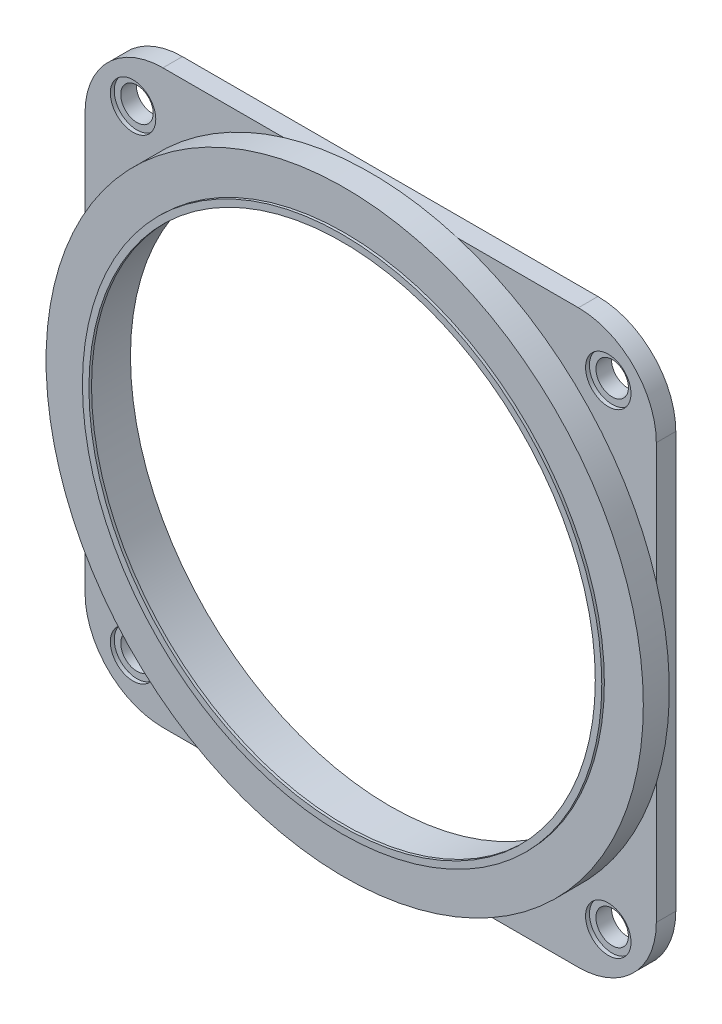
SolidWorks part; units mm, degrees
ref_plane "Alzado" through (0, 0, 0) normal (0, 0, 1) x (1, 0, 0)
ref_plane "Planta" through (0, 0, 0) normal (0, 1, 0) x (1, 0, 0)
ref_plane "Vista lateral" through (0, 0, 0) normal (1, 0, 0) x (0, 0, -1)
sketch "Croquis1" plane through (0, 0, 0) normal (0, 0, 1) x (1, 0, 0)
  line L1 (-16, 22) -> (16, 22)
  line L2 (-22, 16) -> (-22, -16)
  line L3 (-16, -22) -> (16, -22)
  line L4 (22, 16) -> (22, -16)
  line L5 (-22, 22) -> (22, -22) construction
  line L6 (-22, -22) -> (22, 22) construction
  arc A0 (-22, -16) -> (-16, -22) centre (-16, -16) ccw
  arc A1 (16, -22) -> (22, -16) centre (16, -16) ccw
  arc A2 (16, 22) -> (22, 16) centre (16, 16) cw
  arc A3 (-16, 22) -> (-22, 16) centre (-16, 16) ccw
  point P0 (0, 0)
  dimension "D3" = 6
extrude "Saliente-Extruir1" add sketch "Croquis1" along normal blind 1.5
sketch "Croquis2" plane through (0, 0, 1.5) normal (0, 0, 1) x (1, 0, 0)
  circle A0 centre (0, 0) radius 20
  dimension "D1" = 40
extrude "Cortar-Extruir1" cut sketch "Croquis2" against normal through all
sketch "Croquis3" plane through (0, 0, 1.5) normal (0, 0, 1) x (1, 0, 0)
  circle A0 centre (0, 0) radius 20 construction
  circle A1 centre (0, 0) radius 20
  circle A2 centre (0, 0) radius 23
  dimension "D1" = 46
extrude "Saliente-Extruir2" add sketch "Croquis3" along normal blind 2
sketch "Croquis4" plane through (0, 0, 1.5) normal (0, 0, 1) x (1, 0, 0)
  line L0 (22, 16) -> (18.3, 16) construction
  line L1 (18.3, 21.5417) -> (18.3, 18.3) construction
  line L2 (0, 0) -> (0, 9.3365) construction
  line L3 (0, 0) -> (6.6879, 0) construction
  line L4 (16, 22) -> (6.7082, 22) construction
  arc A1 (22, 16) -> (16, 22) centre (16, 16) ccw construction
  circle A2 centre (18.3, 18.3) radius 1.25
  circle A3 centre (-18.3, 18.3) radius 1.25
  circle A4 centre (18.3, -18.3) radius 1.25
  circle A5 centre (-18.3, -18.3) radius 1.25
  dimension "D3" = 2.5
  dimension "D1" = 3.7
  dimension "D2" = 3.7
extrude "Cortar-Extruir2" cut sketch "Croquis4" against normal blind 2
sketch "Croquis6" plane through (0, 0, 1.5) normal (0, 0, 1) x (1, 0, 0)
  circle A0 centre (18.3, 18.3) radius 1.75
  circle A1 centre (-18.3, 18.3) radius 1.75
  circle A2 centre (-18.3, -18.3) radius 1.75
  circle A3 centre (18.3, -18.3) radius 1.75
  dimension "D1" = 3.5
  dimension "D2" = 3.5
  dimension "D3" = 3.5
  dimension "D4" = 3.5
extrude "Cortar-Extruir3" cut sketch "Croquis6" against normal blind 0.3
ref_plane "Plano1" through (0, 0, 3.5) normal (0, 0, 1) x (1, 0, 0)
sketch "Croquis7" plane through (0, 0, 3.5) normal (0, 0, 1) x (1, 0, 0)
  circle A0 centre (0, 0) radius 19.5
  circle A1 centre (0, 0) radius 20 construction
  circle A2 centre (0, 0) radius 20
  dimension "D1" = 39
extrude "Saliente-Extruir3" add sketch "Croquis7" along normal blind 0.2
